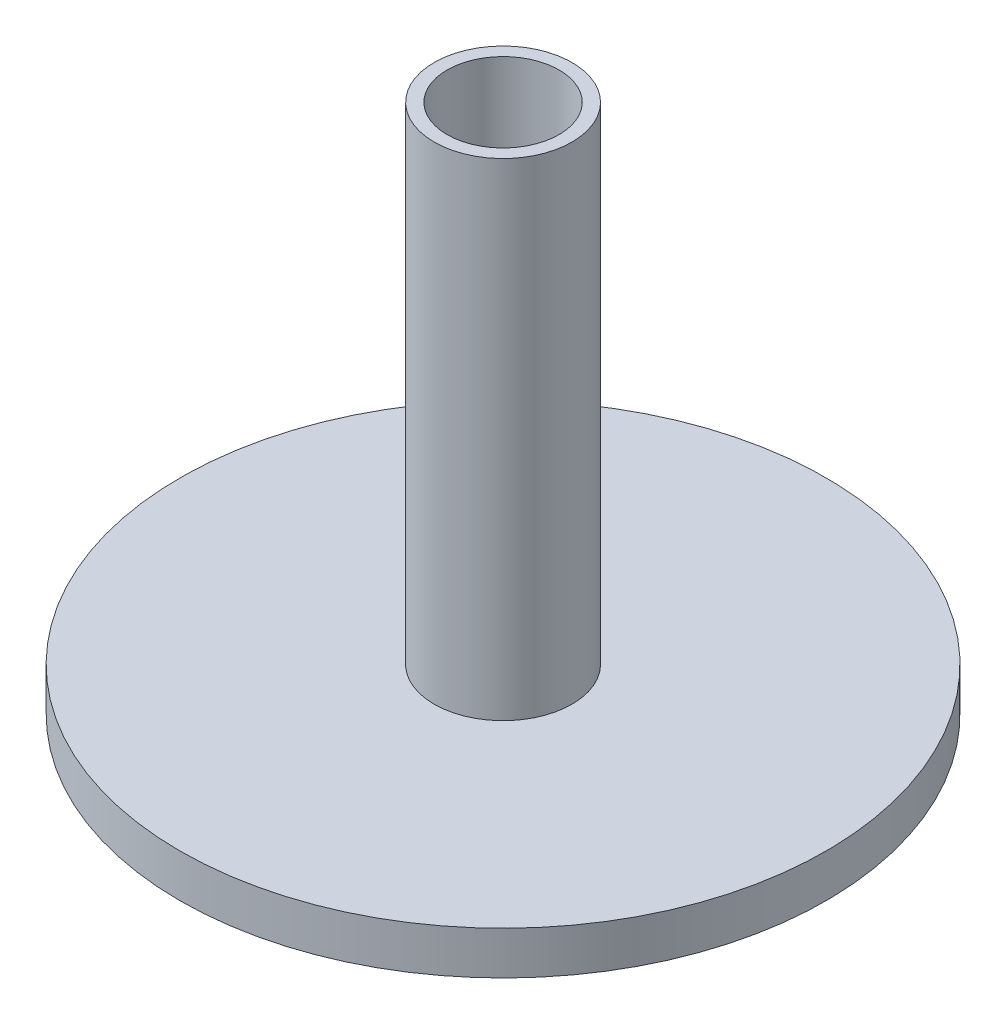
SolidWorks part; units mm, degrees
ref_plane "Front Plane" through (0, 0, 0) normal (0, 0, 1) x (1, 0, 0)
ref_plane "Top Plane" through (0, 0, 0) normal (0, 1, 0) x (1, 0, 0)
ref_plane "Right Plane" through (0, 0, 0) normal (1, 0, 0) x (0, 0, -1)
sketch "Sketch1" plane through (0, 0, 0) normal (0, 1, 0) x (1, 0, 0)
  circle A0 centre (0, 0) radius 75
  dimension "D1" = 150
extrude "Boss-Extrude1" add sketch "Sketch1" along normal blind 10
sketch "Sketch2" plane through (0, 10, 0) normal (0, 1, 0) x (1, 0, 0)
  circle A0 centre (0, 0) radius 13
  circle A1 centre (0, 0) radius 16
  dimension "D1" = 26
  dimension "D2" = 3
extrude "Boss-Extrude2" add sketch "Sketch2" along normal blind 113
